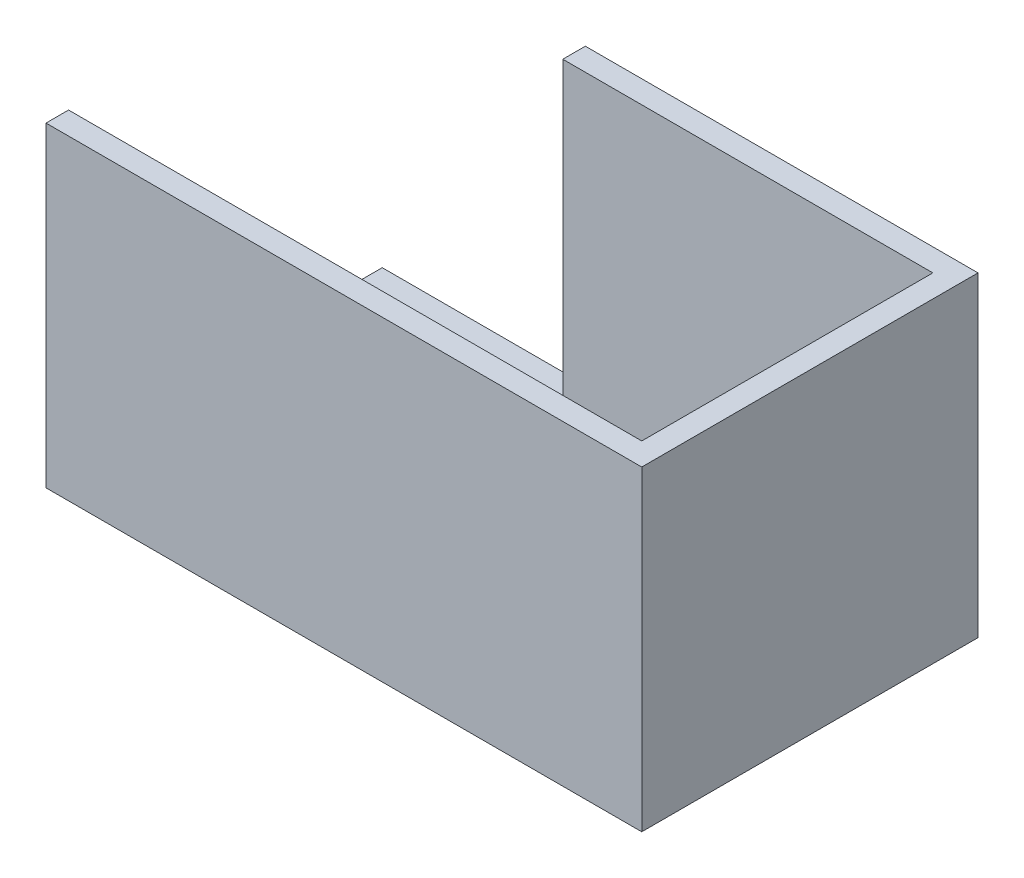
SolidWorks part; units mm, degrees
ref_plane "Front Plane" through (0, 0, 0) normal (0, 0, 1) x (1, 0, 0)
ref_plane "Top Plane" through (0, 0, 0) normal (0, 1, 0) x (1, 0, 0)
ref_plane "Right Plane" through (0, 0, 0) normal (1, 0, 0) x (0, 0, -1)
sketch "Sketch1" plane through (0, 0, 0) normal (0, 1, 0) x (1, 0, 0)
  line L1 (0, 0) -> (52.8, 0)
  line L2 (0, 0) -> (0, -29.8)
  line L3 (0, -29.8) -> (52.8, -29.8)
  line L4 (52.8, 0) -> (52.8, -29.8)
  dimension "D1" = 52.8
  dimension "D2" = 29.8
extrude "Boss-Extrude1" add sketch "Sketch1" along normal blind 2
sketch "Sketch2" plane through (0, 2, 0) normal (0, 1, 0) x (1, 0, 0)
  line L0 (18, -27.8) -> (50.8, -27.8)
  line L1 (50.8, -2) -> (0, -2)
  line L2 (50.8, -27.8) -> (50.8, -23)
  line L3 (50.8, -29.8) -> (50.8, 0) construction
  line L4 (0, 0) -> (0, -29.8)
  line L5 (0, -29.8) -> (52.8, -29.8)
  line L6 (52.8, -29.8) -> (52.8, 0)
  line L7 (52.8, 0) -> (0, 0)
  line L8 (0, 0) -> (0, -2)
  line L9 (18, -29.8) -> (52.8, -29.8)
  line L10 (52.8, -29.8) -> (52.8, -23)
  line L11 (52.8, 0) -> (0, 0)
  line L12 (52.8, -2) -> (0, -2) construction
  line L13 (0, -27.8) -> (52.8, -27.8) construction
  line L17 (50.8, -15) -> (50.8, -2)
  line L18 (52.8, -15) -> (52.8, 0)
  line L19 (52.8, -29.8) -> (52.8, 0) construction
  line L20 (50.8, -23) -> (50.8, -15)
  line L21 (52.8, -23) -> (52.8, -15)
  line L22 (0, -29.8) -> (52.8, -29.8) construction
  line L24 (47.8, -2) -> (47.8, 0)
  line L25 (47.8, -27.8) -> (47.8, -29.8)
  line L26 (50.8, -15) -> (49.4011, -15)
  line L27 (49.4011, -15) -> (49.4011, -23)
  line L28 (49.4011, -23) -> (50.8, -23)
  line L29 (18, -2) -> (18, 0)
  line L30 (18, -27.8) -> (0, -27.8)
  line L31 (0, 0) -> (0, -29.8) construction
  line L32 (0, -27.8) -> (0, -29.8)
  line L33 (0, -29.8) -> (18, -29.8)
  dimension "D6" = 5
  dimension "D1" = 0
  dimension "D2" = 2
  dimension "D3" = 2
  dimension "D4" = 2
extrude "Boss-Extrude2" add sketch "Sketch2" along normal blind 26
